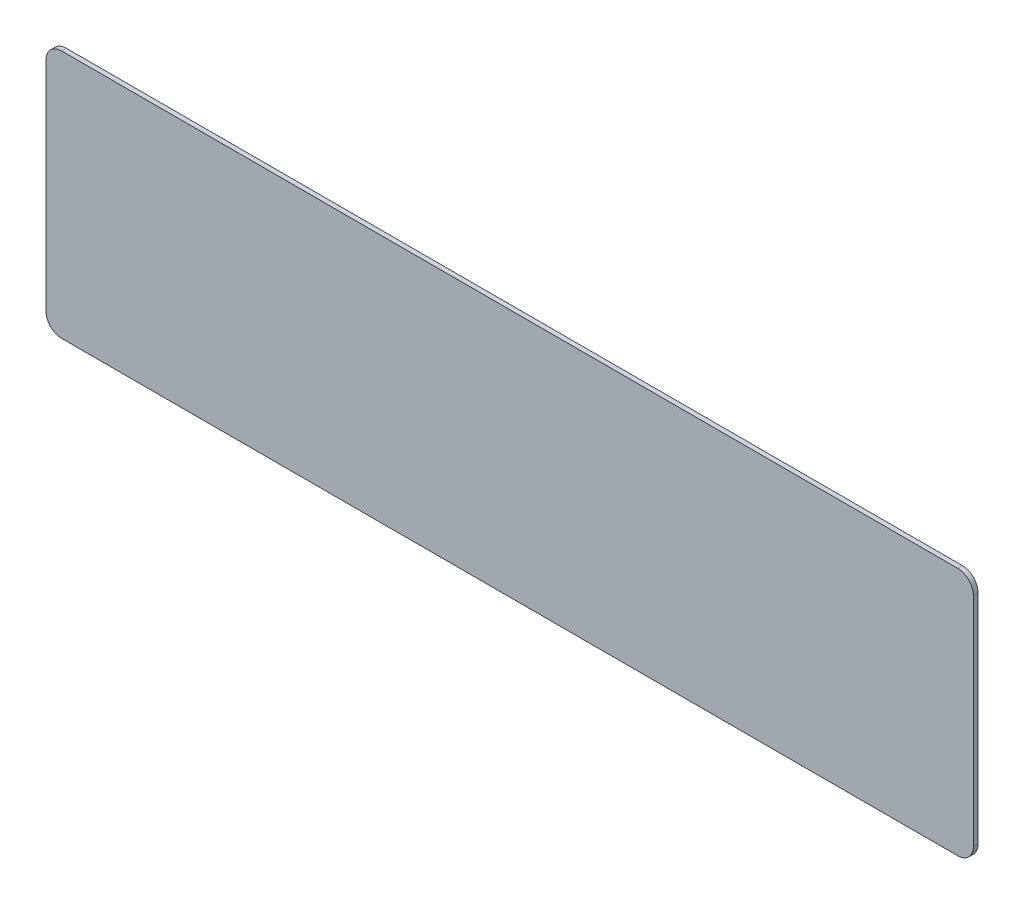
SolidWorks part; units mm, degrees
ref_plane "Plano frontal" through (0, 0, 0) normal (0, 0, 1) x (1, 0, 0)
ref_plane "Plano superior" through (0, 0, 0) normal (0, 1, 0) x (1, 0, 0)
ref_plane "Plano direito" through (0, 0, 0) normal (1, 0, 0) x (0, 0, -1)
sketch "Esboço1" plane through (0, 0, 0) normal (0, 0, 1) x (1, 0, 0)
  line L1 (5, 0) -> (293, 0)
  line L2 (0, 5) -> (0, 75)
  line L3 (5, 80) -> (293, 80)
  line L4 (298, 5) -> (298, 75)
  arc A0 (5, 80) -> (0, 75) centre (5, 75) ccw
  arc A1 (298, 75) -> (293, 80) centre (293, 75) ccw
  arc A2 (293, 0) -> (298, 5) centre (293, 5) ccw
  arc A3 (5, 0) -> (0, 5) centre (5, 5) cw
  point P7 (0, 80)
  point P10 (298, 80)
  point P15 (0, 0)
  dimension "D3" = 5
  dimension "D4" = 5
  dimension "D1" = 298
  dimension "D2" = 80
extrude "Ressalto-extrusão1" add sketch "Esboço1" along normal blind 1.5
